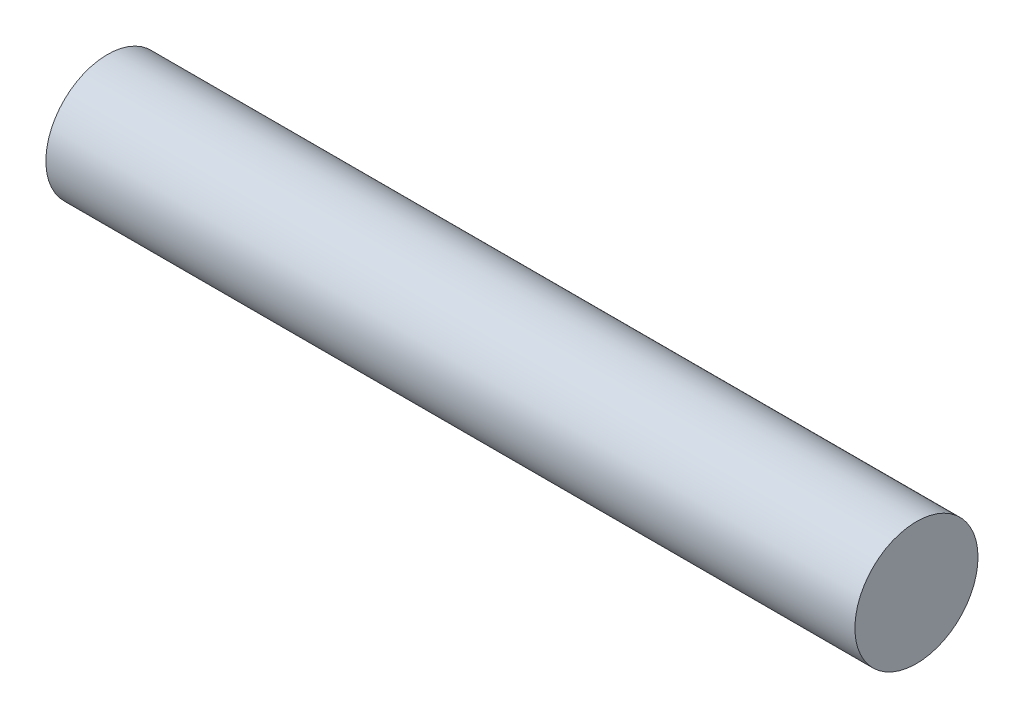
SolidWorks part; units mm, degrees
material "Plain Carbon Steel"
ref_plane "Front Plane" through (0, 0, 0) normal (0, 0, 1) x (1, 0, 0)
ref_plane "Top Plane" through (0, 0, 0) normal (0, 1, 0) x (1, 0, 0)
ref_plane "Right Plane" through (0, 0, 0) normal (1, 0, 0) x (0, 0, -1)
sketch "Sketch1" plane through (0, 0, 0) normal (1, 0, 0) x (0, 0, -1)
  circle A0 centre (0, 0) radius 11.1125
extrude "Boss-Extrude1" add sketch "Sketch1" along normal mid plane 146.05
